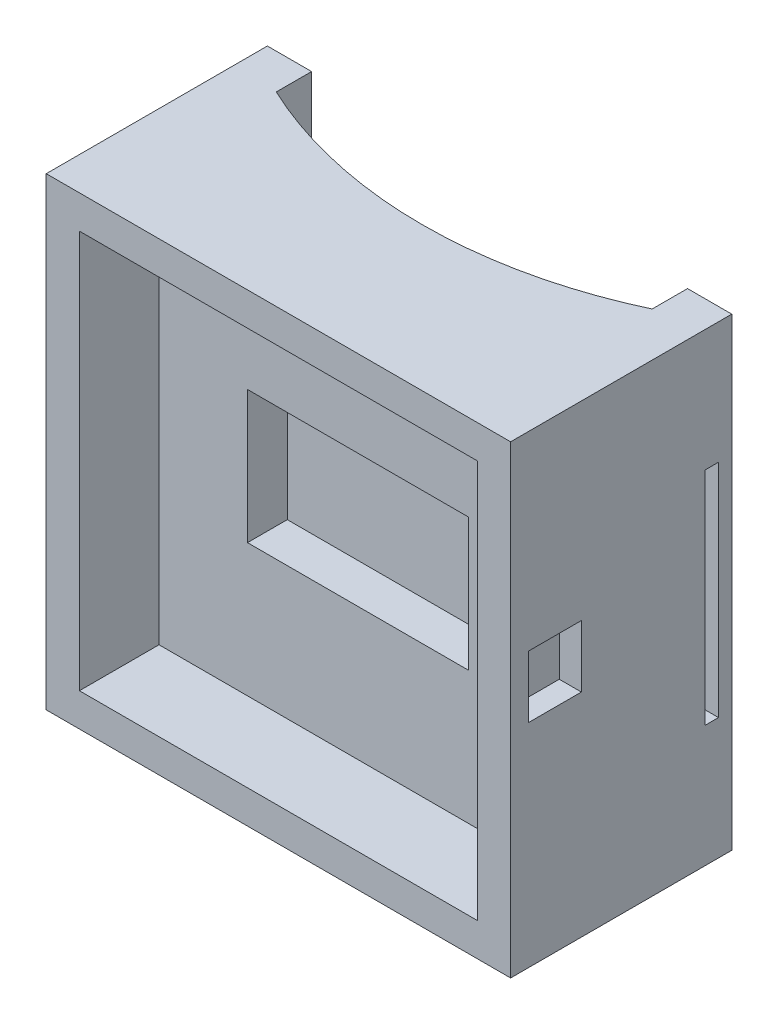
SolidWorks part; units mm, degrees
ref_plane "Front Plane" through (0, 0, 0) normal (0, 0, 1) x (1, 0, 0)
ref_plane "Top Plane" through (0, 0, 0) normal (0, 1, 0) x (1, 0, 0)
ref_plane "Right Plane" through (0, 0, 0) normal (1, 0, 0) x (0, 0, -1)
sketch "Sketch1" plane through (0, 0, 0) normal (0, 0, 1) x (1, 0, 0)
  line L1 (-52.5, 52.5) -> (52.5, 52.5)
  line L2 (-52.5, 52.5) -> (-52.5, -52.5)
  line L3 (-52.5, -52.5) -> (52.5, -52.5)
  line L4 (52.5, 52.5) -> (52.5, -52.5)
  line L5 (-52.5, 52.5) -> (52.5, -52.5) construction
  line L6 (-52.5, -52.5) -> (52.5, 52.5) construction
  point P0 (0, 0)
  dimension "D1" = 105
  dimension "D2" = 105
extrude "Boss-Extrude1" add sketch "Sketch1" along normal blind 50 contours L4 L3 L2 L1
sketch "Sketch2" plane through (0, -52.5, 0) normal (0, -1, 0) x (1, 0, 0)
  line L0 (-42.5, 59.8967) -> (-42.5, -4.9825) construction
  line L1 (42.5, 62.3227) -> (42.5, -8.5904) construction
  line L3 (52.5, 50) -> (52.5, 0) construction
  line L4 (0, 0) -> (0, 53.6576) construction
  line L7 (-52.5, 0) -> (52.5, 0) construction
  line L9 (-42.5, 8) -> (-42.5, 0)
  line L10 (-42.5, 0) -> (42.5, 0)
  line L11 (42.5, 0) -> (42.5, 8)
  arc A0 (-42.5, 8) -> (42.5, 8) centre (0, -82.5193) cw
  dimension "D3" = 100
  dimension "D2" = 10
  dimension "D4" = 8
extrude "Cut-Extrude1" cut sketch "Sketch2" against normal through all
sketch "Sketch3" plane through (0, 0, 50) normal (0, 0, 1) x (1, 0, 0)
  line L1 (-45, 45) -> (45, 45)
  line L2 (-45, 45) -> (-45, -45)
  line L3 (-45, -45) -> (45, -45)
  line L4 (45, 45) -> (45, -45)
  line L5 (-45, 45) -> (45, -45) construction
  line L6 (-45, -45) -> (45, 45) construction
  point P0 (0, 0)
  dimension "D1" = 90
  dimension "D2" = 90
extrude "Cut-Extrude2" cut sketch "Sketch3" against normal blind 18
sketch "Sketch4" plane through (0, 0, 32) normal (0, 0, 1) x (1, 0, 0)
  line L1 (25, -15) -> (-25, -15)
  line L2 (25, -15) -> (25, 15)
  line L3 (25, 15) -> (-25, 15)
  line L4 (-25, -15) -> (-25, 15)
  line L5 (25, -15) -> (-25, 15) construction
  line L6 (25, 15) -> (-25, -15) construction
  point P0 (0, 0)
  dimension "D1" = 50
  dimension "D2" = 30
extrude "Cut-Extrude3" cut sketch "Sketch4" against normal blind 9
sketch "Sketch5" plane through (-52.5, 0, 0) normal (-1, 0, 0) x (0, 0, 1)
  line L0 (0, 0) -> (60.1055, 0) construction
  line L1 (0, 52.5) -> (0, -52.5) construction
  line L3 (3, 25) -> (6, 25)
  line L4 (3, 25) -> (3, -25)
  line L5 (3, -25) -> (6, -25)
  line L6 (6, 25) -> (6, -25)
  line L7 (3, 25) -> (6, -25) construction
  line L8 (3, -25) -> (6, 25) construction
  point P4 (4.5, 0)
  dimension "D1" = 50
  dimension "D2" = 3
  dimension "D3" = 3
extrude "Cut-Extrude4" cut sketch "Sketch5" against normal through all
sketch "Sketch7" plane through (52.5, 0, 0) normal (1, 0, 0) x (0, 0, -1)
  line L0 (-50, 52.5) -> (-50, -52.5) construction
  line L1 (-46, 9.4955) -> (-34, 9.4955)
  line L2 (-46, 9.4955) -> (-46, -4.5045)
  line L3 (-46, -4.5045) -> (-34, -4.5045)
  line L4 (-34, 9.4955) -> (-34, -4.5045)
  line L5 (-46, 9.4955) -> (-34, -4.5045) construction
  line L6 (-46, -4.5045) -> (-34, 9.4955) construction
  point P0 (-40, 2.4955)
  dimension "D1" = 10
  dimension "D2" = 14
  dimension "D3" = 12
extrude "Cut-Extrude5" cut sketch "Sketch7" against normal blind 5
